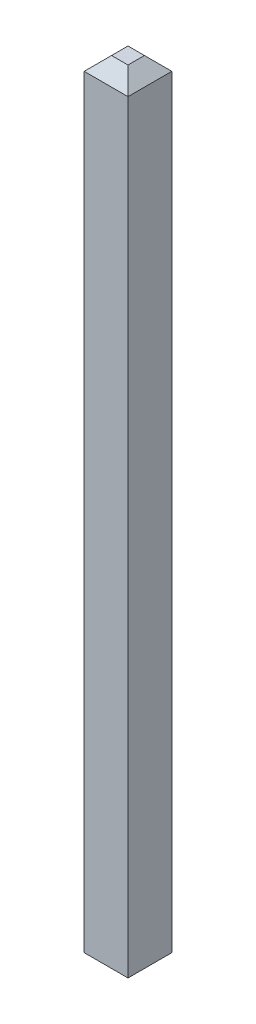
SolidWorks part; units mm, degrees
material "Brass"
ref_plane "Front Plane" through (0, 0, 0) normal (0, 0, 1) x (1, 0, 0)
ref_plane "Top Plane" through (0, 0, 0) normal (0, 1, 0) x (1, 0, 0)
ref_plane "Right Plane" through (0, 0, 0) normal (1, 0, 0) x (0, 0, -1)
sketch "Sketch1" plane through (0, 0, 0) normal (0, 1, 0) x (1, 0, 0)
  line L1 (0.32, -0.32) -> (-0.32, -0.32)
  line L2 (0.32, -0.32) -> (0.32, 0.32)
  line L3 (0.32, 0.32) -> (-0.32, 0.32)
  line L4 (-0.32, -0.32) -> (-0.32, 0.32)
  line L5 (0.32, -0.32) -> (-0.32, 0.32) construction
  line L6 (0.32, 0.32) -> (-0.32, -0.32) construction
  point P0 (0, 0)
  dimension "D1" = 0.64
extrude "Boss-Extrude1" add sketch "Sketch1" along normal blind 11.54
chamfer "Chamfer1" distance 0.2 angle 45 8 edges at (0, 0, 0.32) (0.32, 0, 0) (0, 0, -0.32) (-0.32, 0, 0) (0, 11.54, -0.32) (0.32, 11.54, 0) (0, 11.54, 0.32) (-0.32, 11.54, 0)
